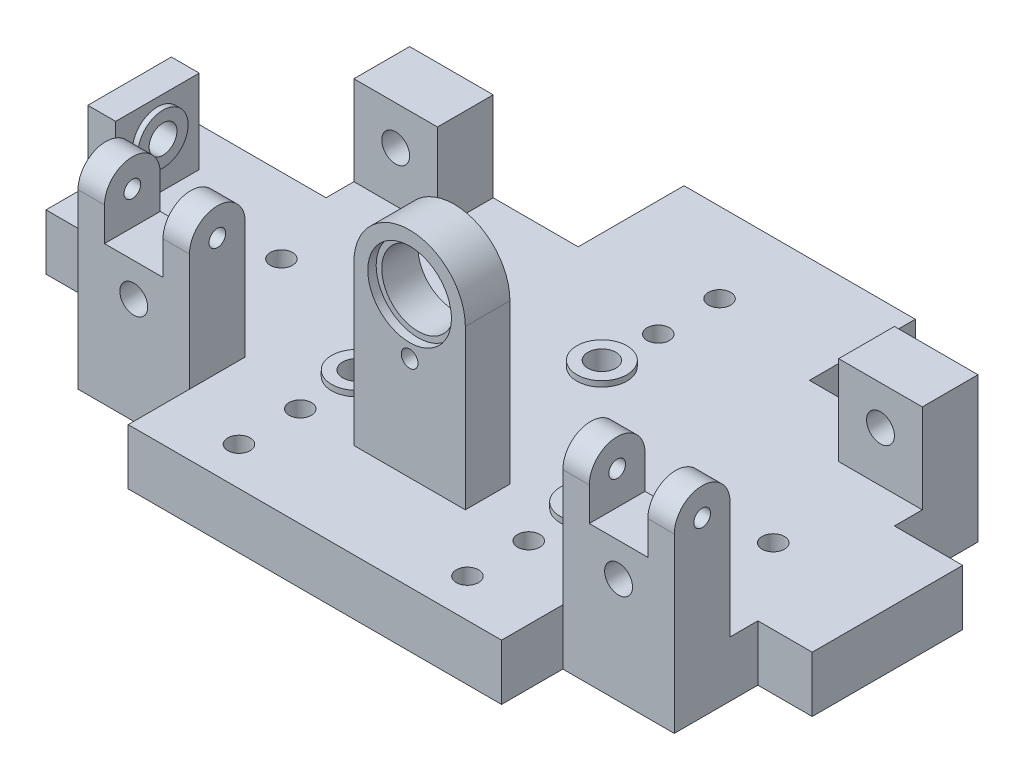
SolidWorks part; units mm, degrees
material "铸造碳钢"
ref_plane "前视基准面" through (0, 0, 0) normal (0, 0, 1) x (1, 0, 0)
ref_plane "上视基准面" through (0, 0, 0) normal (0, 1, 0) x (1, 0, 0)
ref_plane "右视基准面" through (0, 0, 0) normal (1, 0, 0) x (0, 0, -1)
sketch "草图1" plane through (0, 0, 0) normal (0, 1, 0) x (1, 0, 0)
  line L0 (-102, 136) -> (-41.5, 136)
  line L1 (-67, 0) -> (67, 0)
  line L2 (-148.5, 52) -> (-148.5, 106)
  line L4 (126.5, 52) -> (126.5, 106)
  line L5 (-41.5, 136) -> (-41.5, 174)
  line L6 (-41.5, 174) -> (41.5, 174)
  line L7 (41.5, 174) -> (41.5, 136)
  line L8 (41.5, 136) -> (102, 136)
  line L9 (-148.5, 52) -> (-107, 52)
  line L10 (-107, 52) -> (-107, 22)
  line L11 (126.5, 52) -> (107, 52)
  line L12 (107, 52) -> (107, 22)
  line L13 (-107, 22) -> (-67, 22)
  line L14 (-67, 22) -> (-67, 0)
  line L15 (107, 22) -> (67, 22)
  line L16 (67, 22) -> (67, 0)
  line L17 (-102, 136) -> (-102, 106)
  line L18 (-102, 106) -> (-148.5, 106)
  line L19 (102, 136) -> (102, 106)
  line L20 (102, 106) -> (126.5, 106)
  point P18 (0, 0)
  dimension "D1" = 275
  dimension "D2" = 174
  dimension "D3" = 136
  dimension "D4" = 136
  dimension "D5" = 85
  dimension "D6" = 107
  dimension "D7" = 41.5
  dimension "D8" = 19.5
  dimension "D9" = 52
  dimension "D10" = 22
  dimension "D11" = 81.5
  dimension "D12" = 59.5
  dimension "D13" = 30
  dimension "D14" = 24.5
  dimension "D15" = 30
  dimension "D16" = 46.5
extrude "凸台-拉伸1" add sketch "草图1" along normal blind 20
sketch "草图3" plane through (0, 20, 0) normal (0, 1, 0) x (1, 0, 0)
  line L0 (-133.5, 92) -> (-133.5, 62)
  line L1 (-133.5, 62) -> (-143.5, 62)
  line L2 (-143.5, 62) -> (-143.5, 92)
  line L3 (-143.5, 92) -> (-133.5, 92)
  line L4 (-67, 0) -> (67, 0) construction
  line L5 (126.5, 52) -> (126.5, 106) construction
  dimension "D1" = 30
  dimension "D2" = 10
  dimension "D3" = 62
  dimension "D4" = 260
extrude "凸台-拉伸2" add sketch "草图3" along normal blind 30
sketch "草图5" plane through (0, 20, 0) normal (0, 1, 0) x (1, 0, 0)
  line L0 (-107, 42) -> (-107, 22)
  line L1 (-107, 22) -> (-67, 22)
  line L2 (-67, 22) -> (-67, 42)
  line L3 (-67, 42) -> (-107, 42)
  line L4 (67, 42) -> (67, 22)
  line L5 (67, 22) -> (107, 22)
  line L6 (107, 22) -> (107, 42)
  line L7 (107, 42) -> (67, 42)
  line L8 (-67, 0) -> (67, 0) construction
  line L9 (-133.5, 62) -> (-133.5, 92) construction
  dimension "D1" = 20
  dimension "D2" = 40
  dimension "D3" = 20
  dimension "D4" = 40
  dimension "D5" = 42
  dimension "D6" = 42
  dimension "D7" = 26.5
  dimension "D8" = 134
extrude "凸台-拉伸3" add sketch "草图5" along normal blind 42
sketch "草图2" plane through (0, 20, 0) normal (0, 1, 0) x (1, 0, 0)
  line L0 (132.9483, 103) -> (219.6658, 103) construction
  line L1 (123.0215, 56) -> (237.8074, 56) construction
  line L2 (-41, 68.6858) -> (-41, 50.7818) construction
  line L3 (41, 68.6858) -> (41, 53.2784) construction
  line L4 (0, 122.8842) -> (0, 97.7435) construction
  line L6 (-133.5, 62) -> (-133.5, 92) construction
  line L7 (-67, 42) -> (-107, 42) construction
  circle A1 centre (0, 103) radius 5
  circle A2 centre (-41, 56) radius 5
  circle A3 centre (41, 56) radius 5
  dimension "D1" = 10
  dimension "D2" = 10
  dimension "D3" = 10
  dimension "D4" = 14
  dimension "D5" = 47
  dimension "D6" = 92.5
  dimension "D7" = 82
  dimension "D8" = 133.5
extrude "切除-拉伸1" cut sketch "草图2" against normal blind 13
sketch "草图4" plane through (-133.5, 0, 0) normal (1, 0, 0) x (0, 0, -1)
  line L0 (92, 50) -> (92, 20) construction
  line L1 (62, 20) -> (92, 20) construction
  circle A0 centre (77, 38) radius 5
  dimension "D1" = 10
  dimension "D2" = 15
  dimension "D3" = 18
extrude "切除-拉伸2" cut sketch "草图4" against normal up to next
sketch "草图6" plane through (0, 0, -42) normal (0, 0, -1) x (-1, 0, 0)
  line L0 (67, 20) -> (107, 20) construction
  line L1 (-107, 20) -> (-67, 20) construction
  line L2 (67, 62) -> (67, 20) construction
  line L3 (-67, 62) -> (-67, 20) construction
  circle A0 centre (87, 38) radius 5
  circle A1 centre (-87, 38) radius 5
  dimension "D1" = 10
  dimension "D2" = 10
  dimension "D3" = 18
  dimension "D4" = 18
  dimension "D5" = 20
  dimension "D6" = 20
extrude "切除-拉伸3" cut sketch "草图6" against normal up to next
sketch "草图7" plane through (-133.5, 0, 0) normal (1, 0, 0) x (0, 0, -1)
  circle A0 centre (77, 38) radius 9
  circle A1 centre (77, 38) radius 5 construction
  circle A2 centre (77, 38) radius 5
  dimension "D1" = 18
extrude "凸台-拉伸4" add sketch "草图7" along normal blind 2
sketch "草图8" plane through (0, 0, -42) normal (0, 0, -1) x (-1, 0, 0)
  circle A0 centre (87, 38) radius 5 construction
  circle A1 centre (-87, 38) radius 5 construction
  circle A2 centre (87, 38) radius 5
  circle A3 centre (-87, 38) radius 5
  circle A4 centre (-87, 38) radius 9
  circle A5 centre (87, 38) radius 9
  dimension "D1" = 18
  dimension "D2" = 18
extrude "凸台-拉伸5" add sketch "草图8" along normal blind 2
sketch "草图9" plane through (0, 20, 0) normal (0, 1, 0) x (1, 0, 0)
  circle A0 centre (-41, 56) radius 9
  circle A1 centre (0, 103) radius 9
  circle A2 centre (41, 56) radius 9
  circle A3 centre (-41, 56) radius 5 construction
  circle A4 centre (0, 103) radius 5 construction
  circle A5 centre (41, 56) radius 5 construction
  circle A6 centre (-41, 56) radius 5
  circle A7 centre (0, 103) radius 5
  circle A8 centre (41, 56) radius 5
  dimension "D1" = 18
  dimension "D2" = 18
  dimension "D3" = 18
extrude "凸台-拉伸6" add sketch "草图9" along normal blind 2
sketch "草图10" plane through (0, 20, 0) normal (0, 1, 0) x (1, 0, 0)
  line L0 (-67, 42) -> (-107, 42) construction
  line L1 (67, 42) -> (67, 22) construction
  line L2 (107, 42) -> (67, 42) construction
  line L3 (-67, 22) -> (-67, 42) construction
  line L4 (0, 103) -> (0, 157.8551) construction
  line L5 (-133.5, 62) -> (-133.5, 92) construction
  line L6 (-67, 42) -> (-107, 42) construction
  line L7 (107, 42) -> (67, 42) construction
  circle A0 centre (-41, 35.75) radius 4
  circle A1 centre (41, 35.75) radius 4
  circle A2 centre (-41, 13.75) radius 4
  circle A3 centre (41, 13.75) radius 4
  circle A6 centre (-91, 79) radius 4
  circle A7 centre (0, 123.25) radius 4
  circle A8 centre (0, 145.25) radius 4
  circle A9 centre (85.5, 79) radius 4
  circle A10 centre (0, 103) radius 5 construction
  dimension "D2" = 8
  dimension "D3" = 8
  dimension "D7" = 8
  dimension "D8" = 8
  dimension "D10" = 22
  dimension "D11" = 20.25
  dimension "D12" = 42.5
  dimension "D13" = 37
  dimension "D14" = 8
  dimension "D15" = 8
  dimension "D18" = 8
  dimension "D19" = 8
  dimension "D1" = 6.25
  dimension "D4" = 6.25
  dimension "D5" = 26
  dimension "D6" = 26
  dimension "D9" = 22
  dimension "D16" = 37
  dimension "D17" = 176.5
extrude "切除-拉伸4" cut sketch "草图10" against normal through all
sketch "草图11" plane through (0, 20, 0) normal (0, 1, 0) x (1, 0, 0)
  line L0 (-133.5, 62) -> (-133.5, 92) construction
  line L1 (-20, 50) -> (20, 50)
  line L2 (-20, 50) -> (-20, 34)
  line L3 (-20, 34) -> (20, 34)
  line L4 (20, 50) -> (20, 34)
  line L7 (-67, 0) -> (67, 0) construction
  dimension "D1" = 40
  dimension "D2" = 16
  dimension "D3" = 113.5
  dimension "D4" = 34
extrude "凸台-拉伸7" add sketch "草图11" along normal blind 57
sketch "草图12" plane through (0, 77, 0) normal (0, 1, 0) x (1, 0, 0)
  line L5 (0, 34) -> (-20, 34)
  line L6 (-20, 34) -> (20, 34) construction
  line L7 (-20, 34) -> (-20, 50)
  line L8 (-20, 50) -> (0, 50)
  line L9 (20, 50) -> (-20, 50) construction
  line L10 (0, 50) -> (0, 34)
revolve "旋转1" add sketch "草图12" angle 180 about L10
sketch "草图13" plane through (0, 0, -34) normal (0, 0, 1) x (1, 0, 0)
  circle A0 centre (0, 77) radius 15
  arc A1 (20, 77) -> (-20, 77) centre (0, 77) ccw construction
  dimension "D1" = 30
extrude "切除-拉伸5" cut sketch "草图13" against normal blind 3 and the other way through all
sketch "草图14" plane through (0, 0, -37) normal (0, 0, 1) x (1, 0, 0)
  circle A0 centre (0, 77) radius 13
  dimension "D1" = 26
extrude "切除-拉伸6" cut sketch "草图14" against normal up to next
sketch "草图15" plane through (0, 0, -34) normal (0, 0, 1) x (1, 0, 0)
  circle A0 centre (0, 77) radius 20 construction
  circle A1 centre (0, 57) radius 3
  dimension "D1" = 40
  dimension "D2" = 6
extrude "切除-拉伸7" cut sketch "草图15" against normal blind 12
sketch "草图16" plane through (0, 62, 0) normal (0, 1, 0) x (1, 0, 0)
  line L0 (-107, 32) -> (-97.5, 32)
  line L1 (-107, 42) -> (-107, 22) construction
  line L2 (-97.5, 32) -> (-97.5, 42)
  line L3 (-67, 42) -> (-107, 42) construction
  line L4 (-97.5, 42) -> (-107, 42)
  line L5 (-107, 42) -> (-107, 32)
  line L7 (-67, 32) -> (-76.5, 32)
  line L8 (-67, 22) -> (-67, 42) construction
  line L9 (-76.5, 32) -> (-76.5, 42)
  line L10 (-67, 42) -> (-107, 42) construction
  line L11 (-76.5, 42) -> (-67, 42)
  line L12 (-67, 42) -> (-67, 32)
  line L13 (67, 32) -> (76.5, 32)
  line L14 (67, 42) -> (67, 22) construction
  line L15 (76.5, 32) -> (76.5, 42)
  line L16 (107, 42) -> (67, 42) construction
  line L17 (76.5, 42) -> (67, 42)
  line L18 (67, 42) -> (67, 32)
  line L19 (107, 32) -> (97.5, 32)
  line L21 (97.5, 32) -> (97.5, 42)
  line L22 (97.5, 42) -> (107, 42)
  line L23 (107, 42) -> (107, 32)
  dimension "D1" = 9.5
  dimension "D2" = 9.5
  dimension "D3" = 9.5
  dimension "D4" = 9.5
revolve "旋转2" add sketch "草图16" angle 360 about L19
sketch "草图17" plane through (0, 62, 0) normal (0, 1, 0) x (1, 0, 0)
  line L4 (-97.5, 22) -> (-76.5, 22)
  line L5 (-76.5, 22) -> (-76.5, 42)
  line L6 (-76.5, 42) -> (-97.5, 42)
  line L7 (-97.5, 42) -> (-97.5, 22)
  line L8 (-97.5, 22) -> (-76.5, 22)
  line L9 (-76.5, 22) -> (-76.5, 42)
  line L10 (-76.5, 42) -> (-97.5, 42)
  line L11 (-97.5, 42) -> (-97.5, 22)
  line L12 (76.5, 42) -> (76.5, 22)
  line L13 (76.5, 22) -> (97.5, 22)
  line L14 (97.5, 22) -> (97.5, 42)
  line L15 (97.5, 42) -> (76.5, 42)
  line L16 (76.5, 42) -> (76.5, 22)
  line L17 (76.5, 22) -> (97.5, 22)
  line L18 (97.5, 22) -> (97.5, 42)
  line L19 (97.5, 42) -> (76.5, 42)
  dimension "D1" = 0
  dimension "D2" = 0
extrude "切除-拉伸8" cut sketch "草图17" against normal blind 12
sketch "草图18" plane through (-107, 0, 0) normal (-1, 0, 0) x (0, 0, 1)
  circle A1 centre (-32, 62) radius 3
  dimension "D1" = 6
extrude "切除-拉伸9" cut sketch "草图18" against normal up to surface (40 mm away) up to face at (-67, 43.5, -32)
sketch "草图19" plane through (107, 0, 0) normal (1, 0, 0) x (0, 0, -1)
  circle A0 centre (32, 62) radius 3
  dimension "D1" = 6
extrude "切除-拉伸10" cut sketch "草图19" against normal up to surface (40 mm away) up to face at (67, 43.5, -32)
sketch "草图20" plane through (0, 20, 0) normal (0, 1, 0) x (1, 0, 0)
  line L0 (-102, 136) -> (-72, 136)
  line L1 (-72, 136) -> (-72, 116)
  line L2 (-72, 116) -> (-102, 116)
  line L3 (-102, 116) -> (-102, 136)
  line L4 (72, 136) -> (72, 116)
  line L5 (72, 116) -> (102, 116)
  line L6 (102, 116) -> (102, 136)
  line L7 (102, 136) -> (72, 136)
  line L8 (-67, 42) -> (-107, 42) construction
  line L9 (107, 42) -> (67, 42) construction
  line L10 (-67, 22) -> (-67, 42) construction
  line L12 (107, 22) -> (107, 42) construction
  dimension "D1" = 74
  dimension "D2" = 20
  dimension "D3" = 20
  dimension "D4" = 74
  dimension "D5" = 30
  dimension "D6" = 30
  dimension "D7" = 5
  dimension "D8" = 5
extrude "凸台-拉伸8" add sketch "草图20" along normal blind 32
sketch "草图21" plane through (0, 0, -116) normal (0, 0, 1) x (1, 0, 0)
  circle A0 centre (87, 38) radius 5 construction
  circle A1 centre (-87, 38) radius 5 construction
  circle A2 centre (87, 38) radius 5
  circle A3 centre (-87, 38) radius 5
extrude "切除-拉伸11" cut sketch "草图21" against normal up to next
